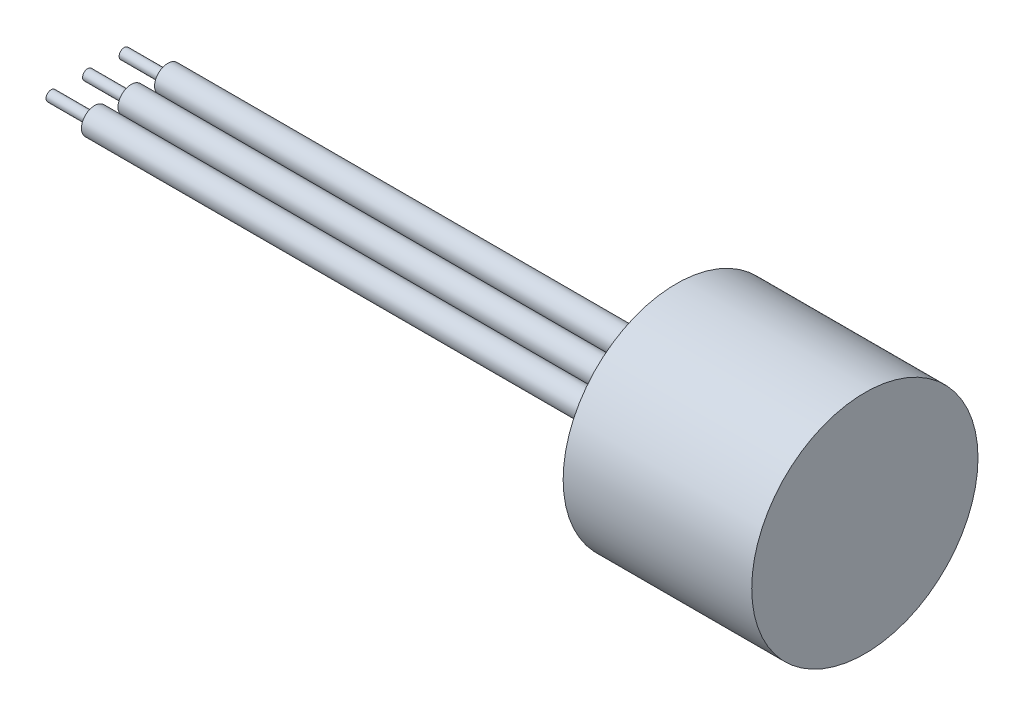
SolidWorks part; units mm, degrees
ref_plane "Front Plane" through (0, 0, 0) normal (0, 0, 1) x (1, 0, 0)
ref_plane "Top Plane" through (0, 0, 0) normal (0, 1, 0) x (1, 0, 0)
ref_plane "Right Plane" through (0, 0, 0) normal (1, 0, 0) x (0, 0, -1)
ref_plane "Plane1" through (0, 0, -0.0942) normal (0, 0, 1) x (1, 0, 0)
sketch "Sketch1" plane through (0, 0, -0.0942) normal (0, 0, 1) x (1, 0, 0)
  line L0 (35.6108, -12.1918) -> (35.6108, -5.0804)
  line L1 (35.6108, -5.0804) -> (54.6608, -5.0804)
  line L2 (54.6608, -5.0804) -> (54.6608, -2.7943)
  line L3 (54.6608, -2.7943) -> (39.0398, -2.7942)
  line L4 (39.0398, -2.7942) -> (37.5158, -1.2702)
  line L5 (37.5158, -1.2702) -> (37.5158, 0.3809)
  line L6 (37.5158, 0.3809) -> (58.4708, 0.3809)
  line L7 (58.4708, 0.3809) -> (58.4708, -12.1918)
  line L8 (58.4708, -12.1918) -> (35.6108, -12.1918)
  line L9 (58.4708, -12.1918) -> (35.6108, -12.1918) construction
revolve "Revolve1" add sketch "Sketch1" angle 360 about L9
ref_plane "Plane2" through (0, -12.1918, 0) normal (0, 1, 0) x (1, 0, 0)
sketch "Sketch2" plane through (0, -12.1918, 0) normal (0, 1, 0) x (1, 0, 0)
  line L0 (-27.8892, -3.9698) -> (-27.8892, -3.3983)
  line L1 (-27.8892, -3.3983) -> (-23.0632, -3.3983)
  line L2 (-23.0632, -3.3983) -> (-23.0632, -2.5093)
  line L3 (-23.0632, -2.5093) -> (35.6108, -2.5093)
  line L4 (35.6108, -2.5093) -> (35.6108, -3.9698)
  line L5 (35.6108, -3.9698) -> (-27.8892, -3.9698)
  line L6 (35.6108, -3.9698) -> (-27.8892, -3.9698) construction
revolve "Revolve2" add sketch "Sketch2" angle 360 about L6
ref_plane "Plane3" through (0, -12.1918, 0) normal (0, 1, 0) x (1, 0, 0)
sketch "Sketch3" plane through (0, -12.1918, 0) normal (0, 1, 0) x (1, 0, 0)
  line L0 (-27.8892, 4.1582) -> (-27.8892, 4.7297)
  line L1 (-27.8892, 4.7297) -> (-23.0632, 4.7297)
  line L2 (-23.0632, 4.7297) -> (-23.0632, 5.6187)
  line L3 (-23.0632, 5.6187) -> (35.6108, 5.6187)
  line L4 (35.6108, 5.6187) -> (35.6108, 4.1582)
  line L5 (35.6108, 4.1582) -> (-27.8892, 4.1582)
  line L6 (35.6108, 4.1582) -> (-27.8892, 4.1582) construction
revolve "Revolve3" add sketch "Sketch3" angle 360 about L6
ref_plane "Plane4" through (0, -12.1918, 0) normal (0, 1, 0) x (1, 0, 0)
sketch "Sketch4" plane through (0, -12.1918, 0) normal (0, 1, 0) x (1, 0, 0)
  line L0 (-27.8892, 0.0942) -> (-27.8892, 0.6657)
  line L1 (-27.8892, 0.6657) -> (-23.0632, 0.6657)
  line L2 (-23.0632, 0.6657) -> (-23.0632, 1.5547)
  line L3 (-23.0632, 1.5547) -> (35.6108, 1.5547)
  line L4 (35.6108, 1.5547) -> (35.6108, 0.0942)
  line L5 (35.6108, 0.0942) -> (-27.8892, 0.0942)
  line L6 (35.6108, 0.0942) -> (-27.8892, 0.0942) construction
revolve "Revolve4" add sketch "Sketch4" angle 360 about L6
